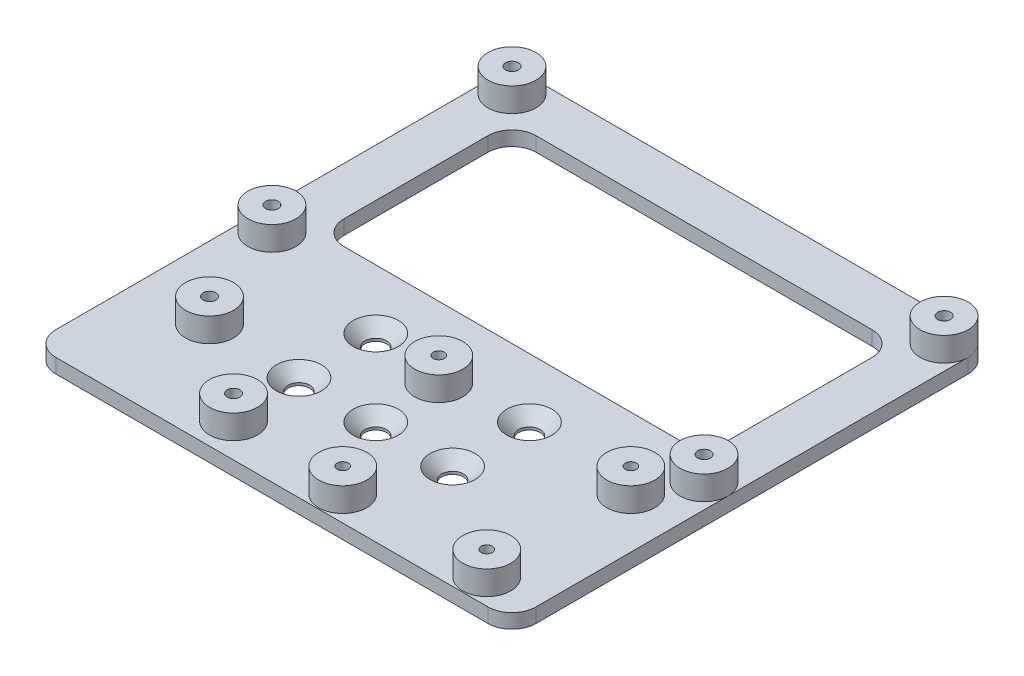
SolidWorks part; units mm, degrees
ref_plane "Front Plane" through (0, 0, 0) normal (0, 0, 1) x (1, 0, 0)
ref_plane "Top Plane" through (0, 0, 0) normal (0, 1, 0) x (1, 0, 0)
ref_plane "Right Plane" through (0, 0, 0) normal (1, 0, 0) x (0, 0, -1)
sketch "Sketch1" plane through (0, 0, 0) normal (0, 1, 0) x (1, 0, 0)
  line L1 (-50, -50) -> (50, -50)
  line L2 (-50, -50) -> (-50, 50)
  line L3 (-50, 50) -> (50, 50)
  line L4 (50, -50) -> (50, 50)
  line L5 (-50, -50) -> (50, 50) construction
  line L6 (-50, 50) -> (50, -50) construction
  point P0 (0, 0)
  dimension "D1" = 100
  dimension "D2" = 100
extrude "Boss-Extrude1" add sketch "Sketch1" along normal blind 3
sketch "Sketch4" plane through (0, 3, 0) normal (0, 1, 0) x (1, 0, 0)
  line L0 (-11.0794, 45) -> (49988.9206, 45) construction
  line L1 (-29.0274, -5) -> (49970.9726, -5) construction
  line L2 (-45, 40.1968) -> (-45, -49959.8032) construction
  line L3 (45, 45.2283) -> (45, -49954.7717) construction
  line L4 (0, 0) -> (0, 50000) construction
  line L5 (50, 50) -> (-50, 50) construction
  circle A0 centre (-45, 45) radius 5
  circle A1 centre (-45, -5) radius 5
  circle A2 centre (45, -5) radius 5
  circle A3 centre (45, 45) radius 5
  dimension "D1" = 10
  dimension "D2" = 90
  dimension "D3" = 50
  dimension "D4" = 5
extrude "Boss-Extrude2" add sketch "Sketch4" along normal blind 5
sketch "Sketch6" plane through (0, 3, 0) normal (0, 1, 0) x (1, 0, 0)
  circle A0 centre (39.5, -44.75) radius 5
  circle A1 centre (39.5, -14.75) radius 5
  circle A2 centre (9.5, -44.75) radius 5
  circle A3 centre (-0.5, -14.75) radius 5
  circle A4 centre (45, -5) radius 5 construction
  circle A5 centre (-35, -28) radius 5
  circle A6 centre (-15, -43) radius 5
extrude "Boss-Extrude3" add sketch "Sketch6" along normal blind 5
sketch "Sketch5" plane through (0, 8, 0) normal (0, 1, 0) x (1, 0, 0)
  circle A0 centre (-45, 45) radius 1.325
  circle A1 centre (45, 45) radius 1.325
  circle A2 centre (45, -5) radius 1.325
  circle A3 centre (-45, -5) radius 1.325
  circle A4 centre (39.5, -14.75) radius 1.15
  circle A5 centre (39.5, -44.75) radius 1.15
  circle A6 centre (9.5, -44.75) radius 1.15
  circle A7 centre (-0.5, -14.75) radius 1.15
  circle A8 centre (-35, -28) radius 1.325
  circle A9 centre (-15, -43) radius 1.325
  dimension "D1" = 2.65
  dimension "D2" = 2.3
extrude "Cut-Extrude1" cut sketch "Sketch5" against normal through all
sketch "Sketch7" plane through (0, 3, 0) normal (0, 1, 0) x (1, 0, 0)
  line L0 (-50, 20) -> (49950, 20) construction
  line L1 (-40, 40) -> (40, 40)
  line L2 (-40, 40) -> (-40, 0)
  line L3 (-40, 0) -> (40, 0)
  line L4 (40, 40) -> (40, 0)
  line L5 (-50, 45) -> (-50, -5) construction
  line L6 (50, -5) -> (50, 45) construction
  line L7 (0, 50) -> (0, -49950) construction
  line L8 (45, 50) -> (-45, 50) construction
  point P8 (-50, 20)
  point P11 (50, 20)
  point P16 (0, 50)
  dimension "D1" = 40
  dimension "D2" = 80
extrude "Cut-Extrude2" cut sketch "Sketch7" against normal through all
fillet "Fillet2" radius 5 8 edges at (50, 1.5, -50) (-50, 1.5, -50) (-50, 1.5, 50) (50, 1.5, 50) (40, 1.5, 0) (40, 1.5, -40) (-40, 1.5, -40) (-40, 1.5, 0)
sketch "Sketch9" plane through (0, 3, 0) normal (0, 1, 0) x (1, 0, 0)
  circle A0 centre (-16, -28.3727) radius 2.4
  circle A1 centre (16, -28.3727) radius 2.4
  circle A2 centre (0, -28.3727) radius 2.4
  circle A3 centre (0, -28.3727) radius 2.4 construction
  circle A4 centre (-16, -28.3727) radius 2.4 construction
  circle A5 centre (16, -28.3727) radius 2.4 construction
  circle A6 centre (-16, -12.3727) radius 2.4
  circle A7 centre (16, -12.3727) radius 2.4
  circle A8 centre (16, -12.3727) radius 2.4 construction
  circle A9 centre (-16, -12.3727) radius 2.4 construction
hole_wizard "CSK for M4 Countersunk Flat Head Screw1" positions "Sketch12" profile "Sketch11" countersink size "M4" standard "ISO" end condition through all
sketch "Sketch12" plane through (0, 3, 0) normal (0, 1, 0) x (1, 0, 0)
  circle A0 centre (-16, -28.3727) radius 2.4 construction
  circle A1 centre (-16, -12.3727) radius 2.4 construction
  circle A2 centre (16, -12.3727) radius 2.4 construction
  circle A3 centre (0, -28.3727) radius 2.4 construction
  circle A4 centre (16, -28.3727) radius 2.4 construction
  point P0 (-16, -12.3727)
  point P2 (-16, -28.3727)
  point P4 (0, -28.3727)
  point P6 (16, -28.3727)
  point P8 (16, -12.3727)
sketch "Sketch11" plane through (-16, 3, 12.3727) normal (1, 0, 0) x (0, 0, 1)
  line L0 (0, 0) -> (0, 3)
  line L1 (0, 3) -> (2.25, 3)
  line L2 (2.25, 3) -> (2.25, 2.45)
  line L3 (2.25, 2.45) -> (4.7, 0)
  line L5 (4.7, 0) -> (0, 0)
  line L6 (-2.25, 2.45) -> (-4.7, 0) construction
  line L11 (0, -6.35) -> (0, 107.95) construction
  dimension "Thru Hole Dia." = 4.5
  dimension "Thru Hole Depth" = 3
  dimension "Near C'Sink Dia." = 9.4
  dimension "Near C'Sink Angle" = 90
